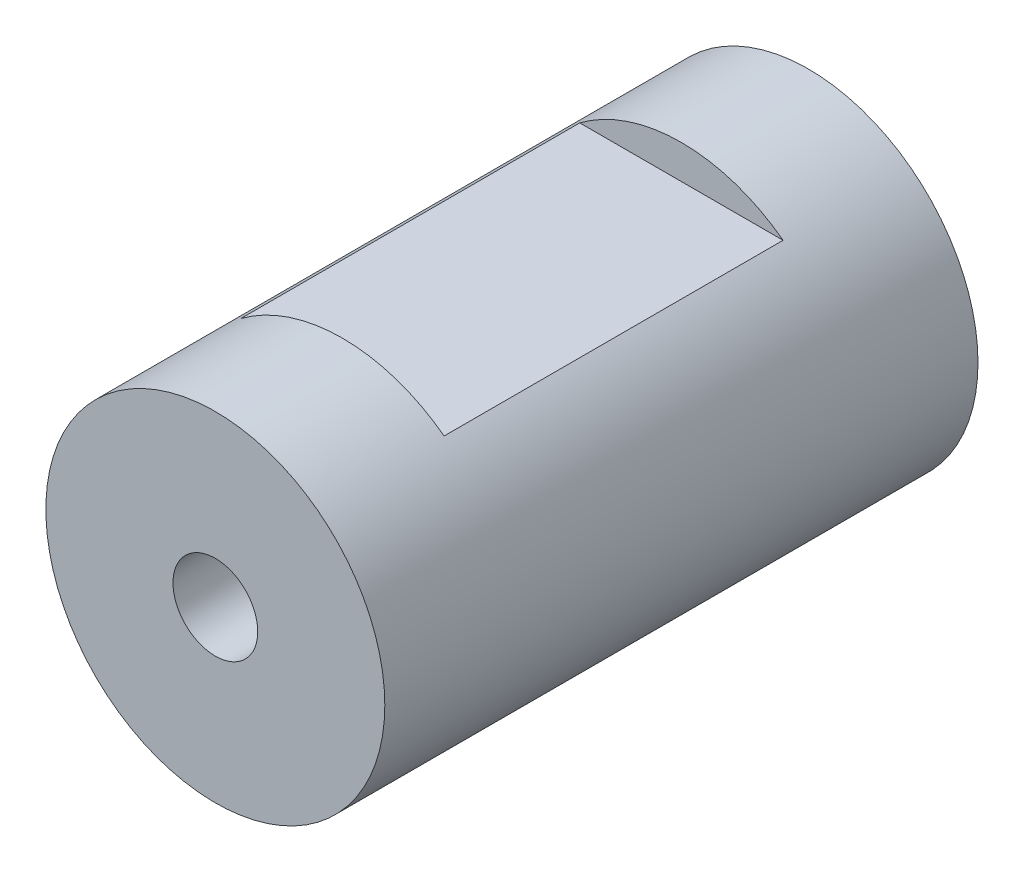
SolidWorks part; units mm, degrees
ref_plane "Front Plane" through (0, 0, 0) normal (0, 0, 1) x (1, 0, 0)
ref_plane "Top Plane" through (0, 0, 0) normal (0, 1, 0) x (1, 0, 0)
ref_plane "Right Plane" through (0, 0, 0) normal (1, 0, 0) x (0, 0, -1)
sketch "Sketch1" plane through (0, 0, 0) normal (0, 0, 1) x (1, 0, 0)
  circle A0 centre (0, 0) radius 20
  dimension "D1" = 40
extrude "Boss-Extrude1" add sketch "Sketch1" against normal mid plane 70
sketch "Sketch2" plane through (0, 0, 0) normal (0, 1, 0) x (1, 0, 0)
  line L0 (0, 35) -> (0, 10)
  line L1 (20, 35) -> (-20, 35) construction
  line L2 (0, 10) -> (12, 10)
  line L3 (12, 10) -> (12, -10)
  line L4 (0, 0) -> (36.8869, 0) construction
  line L5 (0, -35) -> (0, -10)
  line L6 (0, -10) -> (12, -10)
  point P10 (12, 0)
  dimension "D1" = 20
  dimension "D2" = 12
sketch "Sketch3" plane through (0, 0, 35) normal (0, 0, 1) x (1, 0, 0)
  circle A0 centre (0, 0) radius 5
  dimension "D1" = 10
sweep "Cut-Sweep1" cut profiles "Sketch3" path "Sketch2"
sketch "Sketch4" plane through (0, 0, 0) normal (1, 0, 0) x (0, 0, -1)
  line L0 (35, 20) -> (-35, 20) construction
  line L1 (20, 20) -> (-20, 20)
  line L2 (20, 20) -> (20, 16)
  line L3 (20, 16) -> (-20, 16)
  line L4 (-20, 20) -> (-20, 16)
  line L5 (-20, 20) -> (-35, 20) construction
  line L6 (-35, 20) -> (-35, -20) construction
  line L7 (20, 20) -> (35, 20) construction
  line L8 (35, -20) -> (35, 20) construction
  dimension "D1" = 4
  dimension "D2" = 40
extrude "Cut-Extrude1" cut sketch "Sketch4" against normal through all both and the other way through all
